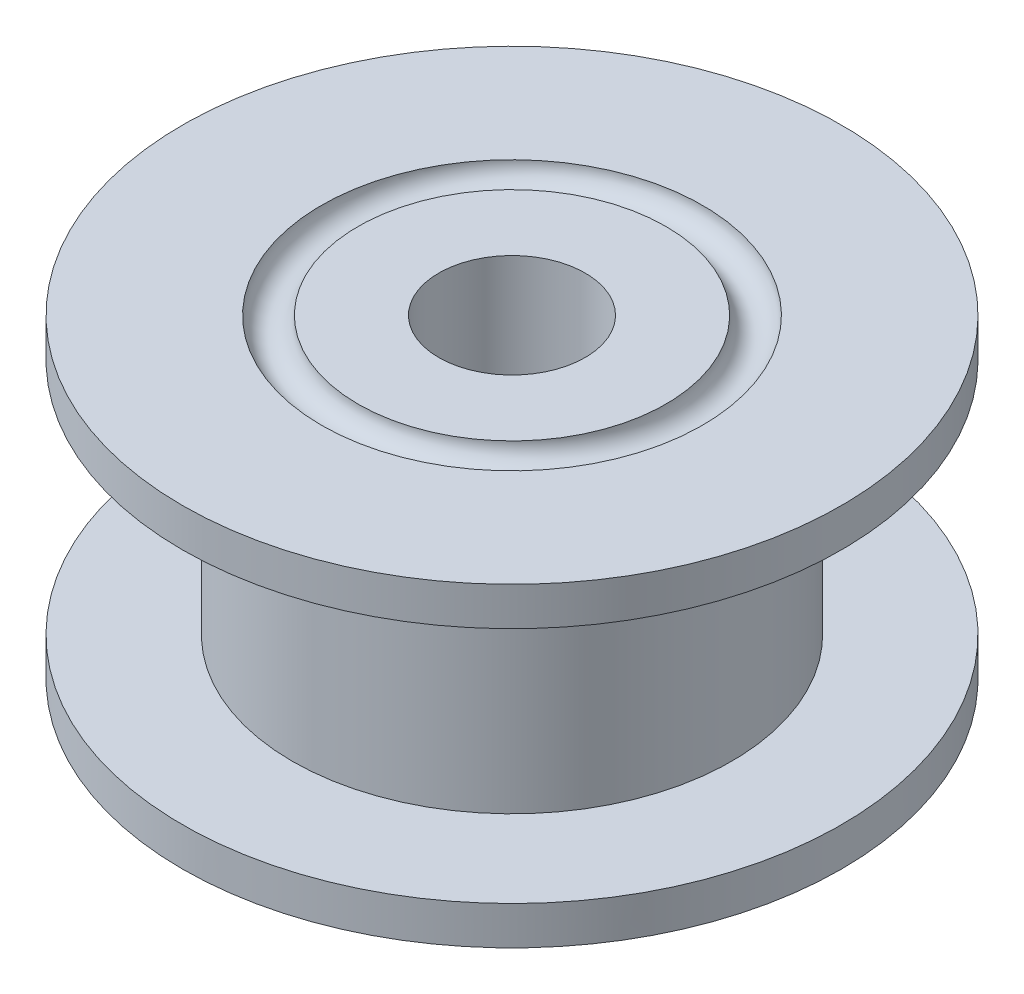
SolidWorks part; units mm, degrees
ref_plane "Alzado" through (0, 0, 0) normal (0, 0, 1) x (1, 0, 0)
ref_plane "Planta" through (0, 0, 0) normal (0, 1, 0) x (1, 0, 0)
ref_plane "Vista lateral" through (0, 0, 0) normal (1, 0, 0) x (0, 0, -1)
sketch "Sketch1" plane through (0, 0, 0) normal (0, 1, 0) x (1, 0, 0)
  circle A0 centre (0, 0) radius 9
extrude "Boss-Extrude1" add sketch "Sketch1" along normal blind 8.6
sketch "Sketch2" plane through (0, 0, 0) normal (0, 0, 1) x (1, 0, 0)
  line L0 (-9, 4.3) -> (5.9504, 4.3) construction
  line L1 (-15.6991, 7.55) -> (-6, 7.55)
  line L2 (-15.6991, 7.55) -> (-15.6991, 1.05)
  line L3 (-15.6991, 1.05) -> (-6, 1.05)
  line L4 (-6, 7.55) -> (-6, 1.05)
  line L5 (-9, 8.6) -> (-9, 0) construction
  line L6 (0, 8.6) -> (0, -0.1328) construction
  line L7 (9, 8.6) -> (-9, 8.6) construction
  dimension "D1" = 6.5
  dimension "D2" = 3.25
  dimension "D3" = 3
revolve "Cut-Revolve1" cut sketch "Sketch2" angle 360 about L6
sketch "Sketch3" plane through (0, 8.6, 0) normal (0, 1, 0) x (1, 0, 0)
  circle A0 centre (0, 0) radius 2
extrude "Cut-Extrude1" cut sketch "Sketch3" against normal through all
sketch "Sketch4" plane through (0, 8.6, 0) normal (0, 1, 0) x (1, 0, 0)
  circle A0 centre (0, 0) radius 4.704
sweep "Cut-Sweep2" cut path "Sketch4" circular profile diameter 1 parameters "D3"=1
sketch "Sketch20" plane through (0, 0, 0) normal (0, -1, 0) x (1, 0, 0)
  circle A0 centre (0, 0) radius 4.7
sweep "Cut-Sweep3" cut path "Sketch20" circular profile diameter 1 parameters "D3"=1
